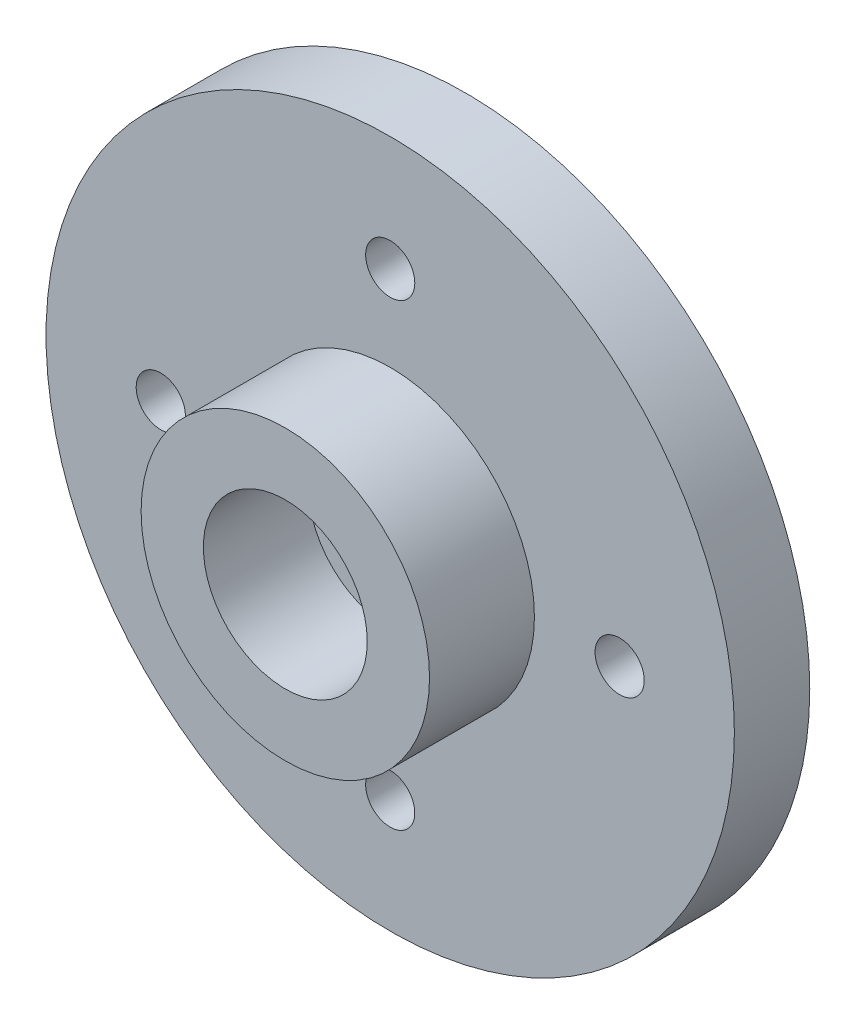
SolidWorks part; units mm, degrees
ref_plane "Front" through (0, 0, 0) normal (0, 0, 1) x (1, 0, 0)
ref_plane "Top" through (0, 0, 0) normal (0, 1, 0) x (1, 0, 0)
ref_plane "Right" through (0, 0, 0) normal (1, 0, 0) x (0, 0, -1)
sketch "Sketch1" plane through (0, 0, 0) normal (0, 0, 1) x (1, 0, 0)
  circle A0 centre (0, 0) radius 10.5
  dimension "D1" = 21
extrude "Boss-Extrude1" add sketch "Sketch1" along normal blind 2.3
sketch "Sketch2" plane through (0, 0, 2.3) normal (0, 0, 1) x (1, 0, 0)
  line L0 (0, 0) -> (0, 10.5) construction
  circle A0 centre (0, 0) radius 10.5 construction
  circle A1 centre (0, 7) radius 0.75
  dimension "D1" = 1.5
  dimension "D2" = 7
extrude "Cut-Extrude1" cut sketch "Sketch2" against normal through all
sketch "Sketch3" plane through (0, 0, 2.3) normal (0, 0, 1) x (1, 0, 0)
  circle A0 centre (0, 0) radius 1.5
  dimension "D1" = 3
extrude "Cut-Extrude2" cut sketch "Sketch3" against normal blind 2.3
pattern_circular "CirPattern1" count 4 over 360 about axis through (0, 0, 0) along (0, 0, 1) of "Cut-Extrude1"
sketch "Sketch4" plane through (0, 0, 2.3) normal (0, 0, 1) x (1, 0, 0)
  circle A0 centre (0, 0) radius 4.4
  circle A1 centre (0, 0) radius 2.5
  dimension "D1" = 8.8
  dimension "D2" = 5
extrude "Boss-Extrude2" add sketch "Sketch4" along normal blind 3.2
